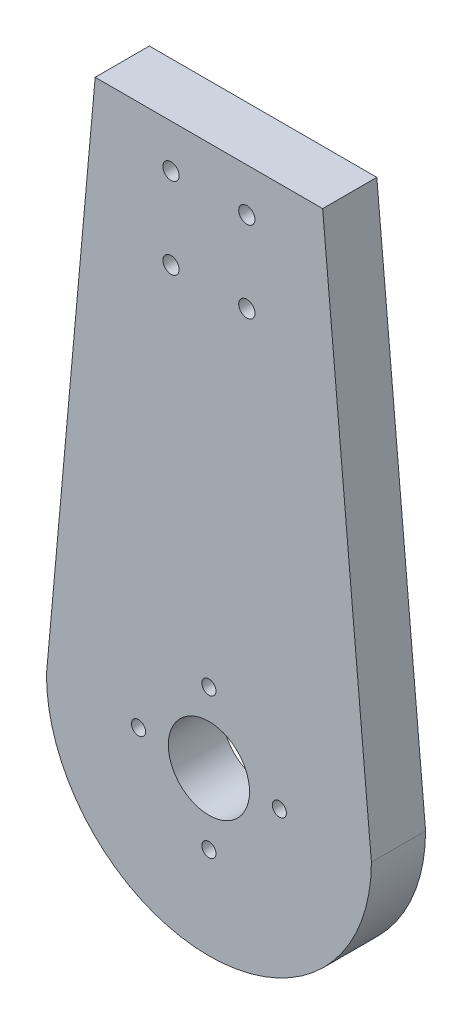
SolidWorks part; units mm, degrees
ref_plane "Front Plane" through (0, 0, 0) normal (0, 0, 1) x (1, 0, 0)
ref_plane "Top Plane" through (0, 0, 0) normal (0, 1, 0) x (1, 0, 0)
ref_plane "Right Plane" through (0, 0, 0) normal (1, 0, 0) x (0, 0, -1)
sketch "Sketch1" plane through (0, 0, 0) normal (0, 0, 1) x (1, 0, 0)
  line L0 (-30, 0) -> (-21, 100)
  line L1 (-21, 100) -> (21, 100)
  line L2 (21, 100) -> (30, 0)
  circle A0 centre (0, 0) radius 30
  point P7 (0, 100)
  dimension "D1" = 60
  dimension "D2" = 42
  dimension "D3" = 100
extrude "Boss-Extrude1" add sketch "Sketch1" along normal blind 10 contours A0 L2 L1 L0 | L2 A0 L0
sketch "Sketch2" plane through (0, 0, 0) normal (0, 0, -1) x (-1, 0, 0)
  line L0 (0, 100) -> (0, 77) construction
  line L1 (21, 100) -> (-21, 100) construction
  line L2 (-7, 77) -> (7, 77) construction
  line L3 (-7, 92) -> (7, 92) construction
  circle A0 centre (7, 92) radius 1.5
  circle A1 centre (7, 77) radius 1.5
  circle A2 centre (-7, 77) radius 1.5
  circle A3 centre (-7, 92) radius 1.5
  point P10 (0, 92)
  point P11 (0, 77)
  dimension "D1" = 7
  dimension "D4" = 3
  dimension "D2" = 8
  dimension "D3" = 15
extrude "Cut-Extrude1" cut sketch "Sketch2" against normal up to next
sketch "Sketch3" plane through (0, 0, 0) normal (0, 0, -1) x (-1, 0, 0)
  circle A0 centre (0, 0) radius 13 construction
  circle A1 centre (0, 13) radius 1.3
  circle A2 centre (13, 0) radius 1.3
  circle A3 centre (0, -13) radius 1.3
  circle A4 centre (-13, 0) radius 1.3
  circle A6 centre (0, 0) radius 7.5
  point P10 (0, 0)
  dimension "D1" = 26
  dimension "D2" = 2.6
  dimension "D3" = 15
extrude "Cut-Extrude2" cut sketch "Sketch3" against normal up to next
